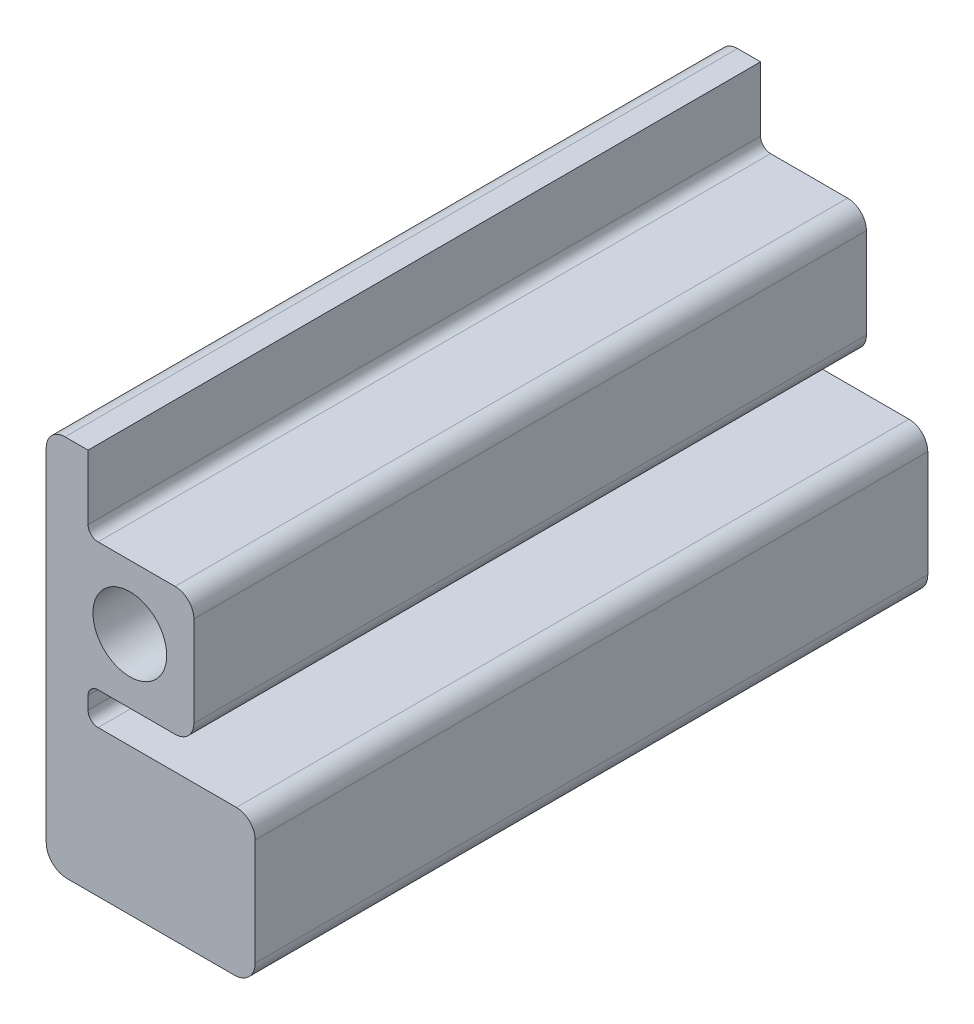
SolidWorks part; units mm, degrees
material "Pink Foam"
ref_plane "Front Plane" through (0, 0, 0) normal (0, 0, 1) x (1, 0, 0)
ref_plane "Top Plane" through (0, 0, 0) normal (0, 1, 0) x (1, 0, 0)
ref_plane "Right Plane" through (0, 0, 0) normal (1, 0, 0) x (0, 0, -1)
sketch "Sketch1" plane through (0, 0, 0) normal (0, 0, 1) x (1, 0, 0)
  line L0 (-25.4, -67.48) -> (-25.4, 36.365)
  line L2 (38.1, -67.48) -> (38.1, -35.095)
  line L3 (32.385, -29.38) -> (-9.652, -29.38)
  line L4 (-12.7, -26.332) -> (-12.7, -22.503)
  line L5 (-9.652, -19.455) -> (0, -19.455)
  line L6 (-9.652, 19.455) -> (0, 19.455)
  line L7 (-12.7, 22.503) -> (-12.7, 26.332)
  line L8 (-9.652, 29.38) -> (32.385, 29.38)
  line L9 (38.1, 35.095) -> (38.1, 36.365)
  line L10 (32.385, 42.08) -> (-19.685, 42.08)
  line L15 (0, -11.2) -> (0, -19.455) construction
  line L16 (0, 11.2) -> (0, 19.455) construction
  line L17 (11.2, 0) -> (19.455, 0) construction
  line L18 (0, 19.455) -> (13.74, 19.455)
  line L19 (19.455, 13.74) -> (19.455, 0)
  line L20 (19.455, 0) -> (19.455, -13.74)
  line L21 (13.74, -19.455) -> (0, -19.455)
  line L24 (31.75, -73.83) -> (-19.05, -73.83)
  circle A0 centre (0, 0) radius 11.2
  arc A3 (-19.685, 42.08) -> (-25.4, 36.365) centre (-19.685, 36.365) ccw
  arc A4 (38.1, 36.365) -> (32.385, 42.08) centre (32.385, 36.365) ccw
  arc A6 (32.385, 29.38) -> (38.1, 35.095) centre (32.385, 35.095) ccw
  arc A7 (38.1, -35.095) -> (32.385, -29.38) centre (32.385, -35.095) ccw
  arc A8 (19.455, -13.74) -> (13.74, -19.455) centre (13.74, -13.74) cw
  arc A9 (13.74, 19.455) -> (19.455, 13.74) centre (13.74, 13.74) cw
  arc A10 (-12.7, 26.332) -> (-9.652, 29.38) centre (-9.652, 26.332) cw
  arc A11 (-9.652, 19.455) -> (-12.7, 22.503) centre (-9.652, 22.503) cw
  arc A12 (-12.7, -22.503) -> (-9.652, -19.455) centre (-9.652, -22.503) cw
  arc A13 (-9.652, -29.38) -> (-12.7, -26.332) centre (-9.652, -26.332) cw
  arc A14 (31.75, -73.83) -> (38.1, -67.48) centre (31.75, -67.48) ccw
  arc A15 (-19.05, -73.83) -> (-25.4, -67.48) centre (-19.05, -67.48) cw
  point P12 (0, 11.2)
  point P20 (0, -11.2)
  point P22 (11.2, 0)
  point P45 (-12.7, 29.38)
  point P48 (-12.7, 19.455)
  point P53 (-12.7, -29.38)
  point P57 (38.1, -73.83)
  point P60 (38.1, -73.83)
  point P63 (-25.4, -73.83)
  dimension "D1" = 22.4
  dimension "D11" = 3.048
  dimension "D9" = 5.715
  dimension "D14" = 5.715
  dimension "D12" = 6.35
  dimension "D2" = 25.4
  dimension "D3" = 8.255
  dimension "D4" = 9.925
  dimension "D5" = 44.45
  dimension "D6" = 9.925
  dimension "D7" = 12.7
  dimension "D8" = 12.7
  dimension "D10" = 63.5
extrude "Boss-Extrude1" add sketch "Sketch1" along normal blind 204.3137
sketch "Sketch2" plane through (0, 0, 204.3137) normal (0, 0, 1) x (1, 0, 0)
  line L0 (38.1, 35.095) -> (38.1, 36.365) construction
  line L1 (19.455, -13.74) -> (38.1, -13.74)
  line L2 (19.455, -13.74) -> (19.455, 42.08)
  line L3 (19.455, 42.08) -> (38.1, 42.08)
  line L4 (38.1, -13.74) -> (38.1, 42.08)
  line L5 (32.385, 42.08) -> (-19.685, 42.08) construction
  line L7 (-12.7, 22.503) -> (19.455, 22.503)
  line L8 (-12.7, 22.503) -> (-12.7, 42.08)
  line L9 (-12.7, 42.08) -> (19.455, 42.08)
  line L10 (19.455, 22.503) -> (19.455, 42.08)
  line M7 (19.455, -13.74) -> (19.455, 13.74)
  line M11 (-12.7, 22.503) -> (-12.7, 26.332)
  arc M12 (-12.7, 26.332) -> (-9.652, 29.38) centre (-9.652, 26.332) cw
  line M13 (-9.652, 29.38) -> (32.385, 29.38)
  arc M14 (32.385, 29.38) -> (38.1, 35.095) centre (32.385, 35.095) ccw
  line M15 (38.1, 35.095) -> (38.1, 36.365)
  arc M16 (38.1, 36.365) -> (32.385, 42.08) centre (32.385, 36.365) ccw
  line M17 (32.385, 42.08) -> (-19.685, 42.08)
extrude "Cut-Extrude1" cut sketch "Sketch2" against normal blind 236.982 contours L2 M13 M14 M15 M16 M17 | L8 L2 M12 M13 M17 | L1 L4 L2 M14 M13 M7 | L4 L3 M16 | L7 L2 M11 M13 M12
